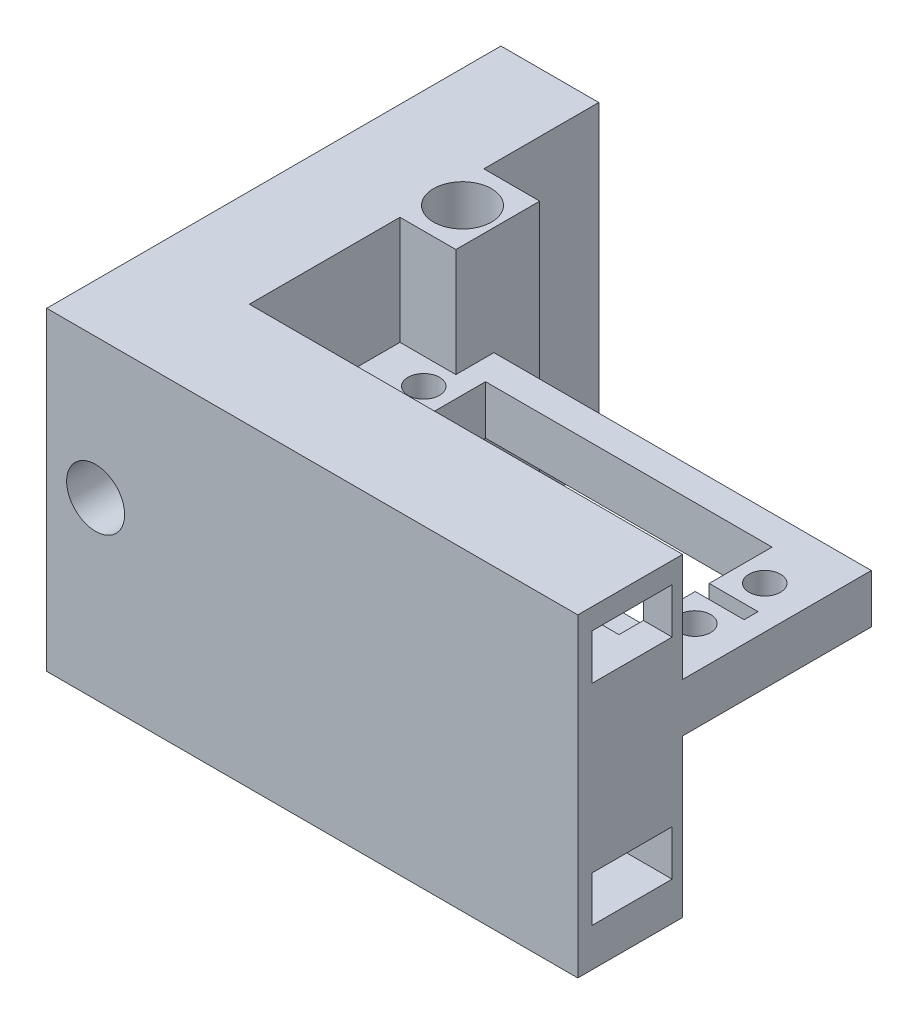
SolidWorks part; units mm, degrees
ref_plane "前视基准面" through (0, 0, 0) normal (0, 0, 1) x (1, 0, 0)
ref_plane "上视基准面" through (0, 0, 0) normal (0, 1, 0) x (1, 0, 0)
ref_plane "右视基准面" through (0, 0, 0) normal (1, 0, 0) x (0, 0, -1)
sketch "草图1" plane through (0, 0, 0) normal (1, 0, 0) x (0, 0, -1)
  line L1 (21.1163, -167.3566) -> (-23.8837, -167.3566)
  line L2 (21.1163, -167.3566) -> (21.1163, -122.3566)
  line L3 (21.1163, -122.3566) -> (-23.8837, -122.3566)
  line L4 (-23.8837, -167.3566) -> (-23.8837, -122.3566)
  dimension "D1" = 45
  dimension "D2" = 45
extrude "凸台-拉伸1" add sketch "草图1" along normal blind 100
sketch "草图2" plane through (0, 0, -21.1163) normal (0, 0, -1) x (-1, 0, 0)
  line L0 (-100, -167.3566) -> (0, -167.3566) construction
  line L1 (-14, -145.8566) -> (-76, -145.8566)
  line L2 (-14, -145.8566) -> (-14, -137.8566)
  line L3 (-14, -137.8566) -> (-76, -137.8566)
  line L4 (-76, -145.8566) -> (-76, -137.8566)
  line L7 (0, -167.3566) -> (0, -122.3566) construction
  dimension "D1" = 62
  dimension "D2" = 21.5
  dimension "D3" = 8
  dimension "D4" = 14
extrude "切除-拉伸1" cut sketch "草图2" against normal blind 30 flip side to cut
sketch "草图3" plane through (0, -137.8566, 0) normal (0, 1, 0) x (1, 0, 0)
  line L0 (14, 21.1163) -> (76, 21.1163) construction
  line L1 (25, 13.9163) -> (66, 13.9163)
  line L2 (25, 13.9163) -> (25, -6.3837)
  line L3 (25, -6.3837) -> (66, -6.3837)
  line L4 (66, 13.9163) -> (66, -6.3837)
  line L5 (14, -8.8837) -> (14, 21.1163) construction
  dimension "D1" = 41
  dimension "D2" = 20.3
  dimension "D3" = 7.2
  dimension "D4" = 11
extrude "切除-拉伸2" cut sketch "草图3" against normal through all
sketch "草图5" plane through (0, 0, 0) normal (-1, 0, 0) x (0, 0, 1)
  line L1 (10.3837, -131.8566) -> (21.8837, -131.8566)
  line L2 (10.3837, -131.8566) -> (10.3837, -125.3566)
  line L3 (10.3837, -125.3566) -> (21.8837, -125.3566)
  line L4 (21.8837, -131.8566) -> (21.8837, -125.3566)
  line L5 (8.8837, -167.3566) -> (8.8837, -122.3566) construction
  line L6 (8.8837, -122.3566) -> (23.8837, -122.3566) construction
  line L7 (10.3837, -161.8566) -> (10.3837, -155.3566)
  line L8 (10.3837, -155.3566) -> (21.8837, -155.3566)
  line L9 (21.8837, -161.8566) -> (21.8837, -155.3566)
  line L10 (10.3837, -161.8566) -> (21.8837, -161.8566)
  dimension "D1" = 6.5
  dimension "D2" = 11.5
  dimension "D3" = 1.5
  dimension "D4" = 3
  dimension "D5" = 2
extrude "切除-拉伸3" cut sketch "草图5" against normal through all
sketch "草图7" plane through (0, -145.8566, 0) normal (0, -1, 0) x (1, 0, 0)
  line L2 (25, 6.3837) -> (25, -13.9163) construction
  line L3 (25, -4.9163) -> (18, -4.9163)
  line L4 (25, -4.9163) -> (25, -2.9163)
  line L5 (25, -2.9163) -> (18, -2.9163)
  line L6 (18, -4.9163) -> (18, -2.9163)
  line L7 (73, -4.9163) -> (66, -4.9163)
  line L8 (73, -4.9163) -> (73, -2.9163)
  line L9 (73, -2.9163) -> (66, -2.9163)
  line L10 (66, -4.9163) -> (66, -2.9163)
  line L11 (66, -13.9163) -> (66, 6.3837) construction
  circle A0 centre (21.15, -8.9163) radius 2.25
  circle A1 centre (21.15, 1.0837) radius 2.25
  circle A2 centre (69.95, -8.9163) radius 2.25
  circle A3 centre (69.95, 1.0837) radius 2.25
  dimension "D1" = 0
  dimension "D6" = 2
  dimension "D7" = 7
  dimension "D8" = 4
  dimension "D9" = 2
  dimension "D4" = 2
  dimension "D5" = 2
extrude "切除-拉伸5" cut sketch "草图7" against normal blind 10
sketch "草图8" plane through (0, 0, 8.8837) normal (0, 0, -1) x (-1, 0, 0)
  line L0 (0, -122.3566) -> (-100, -122.3566) construction
  line L1 (-71.8918, -133.8566) -> (-36.8918, -133.8566)
  line L2 (-71.8918, -133.8566) -> (-71.8918, -123.8566)
  line L3 (-71.8918, -123.8566) -> (-36.8918, -123.8566)
  line L4 (-36.8918, -133.8566) -> (-36.8918, -123.8566)
  dimension "D1" = 1.5
  dimension "D2" = 10
  dimension "D3" = 35
sketch "草图9" plane through (0, 0, -21.1163) normal (0, 0, -1) x (-1, 0, 0)
  line L1 (-76, -137.8566) -> (-14, -137.8566)
  line L2 (-76, -137.8566) -> (-76, -145.8566)
  line L3 (-76, -145.8566) -> (-14, -145.8566)
  line L4 (-14, -137.8566) -> (-14, -145.8566)
extrude "切除-拉伸7" cut sketch "草图9" against normal blind 3
sketch "草图10" plane through (100, 0, 0) normal (1, 0, 0) x (0, 0, -1)
  line L0 (-23.8837, -167.3566) -> (-8.8837, -167.3566) construction
  line L1 (-8.8837, -167.3566) -> (-23.8837, -167.3566)
  line L2 (-8.8837, -167.3566) -> (-8.8837, -122.3566)
  line L3 (-8.8837, -122.3566) -> (-23.8837, -122.3566)
  line L4 (-23.8837, -167.3566) -> (-23.8837, -122.3566)
  line L5 (-8.8837, -167.3566) -> (-8.8837, -122.3566) construction
extrude "切除-拉伸8" cut sketch "草图10" against normal up to surface (24 mm away) up to face at (76, -141.8566, -4.6163)
sketch "草图13" plane through (0, 0, 8.8837) normal (0, 0, -1) x (-1, 0, 0)
  line L1 (0, -122.3566) -> (-76, -122.3566) construction
  line L2 (0, -167.3566) -> (-14, -167.3566)
  line L3 (0, -167.3566) -> (0, -122.3566)
  line L4 (0, -122.3566) -> (-14, -122.3566)
  line L5 (-14, -167.3566) -> (-14, -122.3566)
  line L6 (-14, -145.8566) -> (-14, -137.8566) construction
  dimension "D1" = 0
extrude "凸台-拉伸3" add sketch "草图13" along normal blind 50
sketch "草图14" plane through (0, 0, -41.1163) normal (0, 0, -1) x (-1, 0, 0)
  line L0 (0, -122.3566) -> (-14, -122.3566) construction
  line L1 (0, -167.3566) -> (0, -122.3566) construction
  circle A0 centre (-7, -142.3566) radius 4.15
  dimension "D1" = 8.3
  dimension "D2" = 20
  dimension "D3" = 7
extrude "切除-拉伸9" cut sketch "草图14" against normal through all
sketch "草图15" plane through (14, 0, 0) normal (1, 0, 0) x (0, 0, -1)
  line L0 (41.1163, -122.3566) -> (-8.8837, -122.3566) construction
  line L1 (24.6689, -122.3566) -> (12.6689, -122.3566)
  line L2 (24.6689, -122.3566) -> (24.6689, -167.3566)
  line L3 (24.6689, -167.3566) -> (12.6689, -167.3566)
  line L4 (12.6689, -122.3566) -> (12.6689, -167.3566)
  line L5 (41.1163, -167.3566) -> (-8.8837, -167.3566) construction
  dimension "D1" = 12
extrude "凸台-拉伸4" add sketch "草图15" along normal blind 8
sketch "草图17" plane through (0, -167.3566, 0) normal (0, -1, 0) x (1, 0, 0)
  line L0 (14, -41.1163) -> (0, -41.1163) construction
  line L1 (0, 23.8837) -> (0, -41.1163) construction
  circle A0 centre (17, -18.6163) radius 4.15
  dimension "D1" = 8.3
  dimension "D2" = 22.5
  dimension "D3" = 17
extrude "切除-拉伸11" cut sketch "草图17" against normal through all
extrude "切除-拉伸12" cut sketch "草图8" against normal blind 5
sketch "草图18" plane through (0, -145.8566, 0) normal (0, -1, 0) x (1, 0, 0)
  line L0 (14, 8.8837) -> (14, -12.6689) construction
  line L1 (76, 8.8837) -> (22, 8.8837)
  line L2 (76, 8.8837) -> (76, -18.1163)
  line L3 (76, -18.1163) -> (22, -18.1163)
  line L4 (22, -12.6543) -> (22, -18.1163)
  line L5 (22, 8.8837) -> (14, 8.8837)
  line L7 (22, -12.6543) -> (14, -12.6543)
  line L8 (14, 8.8837) -> (14, -12.6543)
extrude "切除-拉伸14" cut sketch "草图18" against normal blind 1
